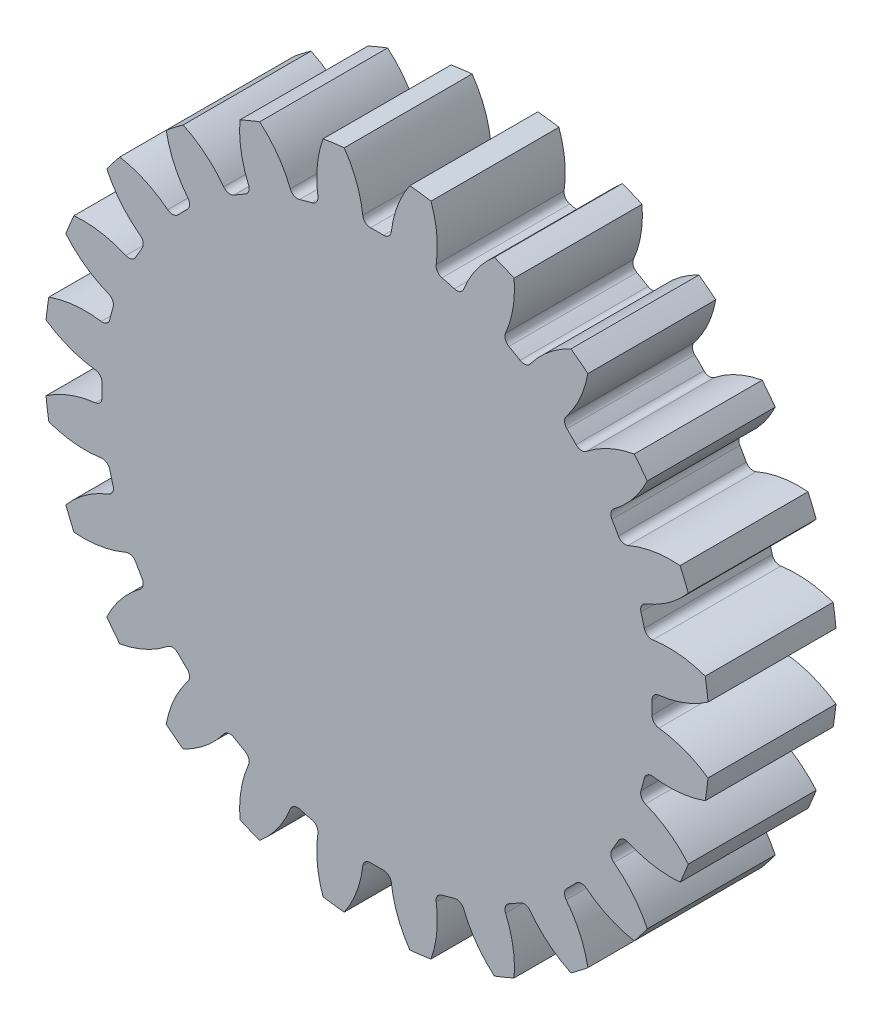
SolidWorks part; units mm, degrees
ref_plane "Front" through (0, 0, 0) normal (0, 0, 1) x (1, 0, 0)
ref_plane "Top" through (0, 0, 0) normal (0, 1, 0) x (1, 0, 0)
ref_plane "Right" through (0, 0, 0) normal (1, 0, 0) x (0, 0, -1)
sketch "Sketch2" plane through (0, 0, 0) normal (0, 0, 1) x (1, 0, 0)
  circle A0 centre (0, 0) radius 21.5
  circle A1 centre (0, 0) radius 24
  circle A2 centre (0, 0) radius 26
  dimension "D1" = 48
  dimension "D2" = 52
  dimension "D3" = 4.5
extrude "Boss-Extrude1" add sketch "Sketch2" along normal mid plane 10 contours A2
sketch "Sketch3" plane through (0, 0, 0) normal (0, 0, 1) x (1, 0, 0)
  line L0 (0, 0) -> (0, 26) construction
  line L1 (-1.5697, 23.9486) -> (1.5697, 23.9486) construction
  line L2 (0, 0) -> (-1.0694, 21.4734) construction
  line L3 (0, 19.636) -> (-2.6334, 26.8713) construction
  line L4 (0, 0) -> (3.3937, 25.7776) construction
  line L5 (1.5697, 23.9486) -> (4.6822, 23.5388) construction
  circle A0 centre (0, 0) radius 26 construction
  arc A1 (-1.0694, 21.4734) -> (-3.3054, 26.7969) centre (-9.5277, 21.0521) ccw
  arc A2 (1.0694, 21.4734) -> (3.3054, 26.7969) centre (9.5277, 21.0521) cw
  circle A3 centre (0, 0) radius 21.5 construction
  arc A4 (1.0694, 21.4734) -> (-1.0694, 21.4734) centre (0, 0) ccw
  circle A6 centre (0, 0) radius 24 construction
  circle A7 centre (0, 0) radius 27
  arc A8 (3.3054, 26.7969) -> (-3.3054, 26.7969) centre (0, 0) ccw
  circle A9 centre (0, 0) radius 26 construction
  dimension "D2" = 20
  dimension "D3" = 7.5
  dimension "D1" = 1
extrude "Cut-Extrude1" cut sketch "Sketch3" against normal through all both and the other way through all contours A8 A1 A4 A2
fillet "Fillet1" radius 0.6 2 edges at (1.0694, 21.4734, 0) (-1.0694, 21.4734, 0)
pattern_circular "CirPattern1" count 24 over 360 about axis through (0, 0, 0) along (0, 0, 1) of "Fillet1", "Cut-Extrude1"
equation "\"teeth\"= 24"
equation "\"module\"= 2mm"
equation "\"D1@Sketch2\"=\"module\"*\"teeth\""
equation "\"D2@Sketch2\"=(\"teeth\"+2)*\"module\""
equation "\"pressure_angle\"= 20deg"
equation "\"D2@Sketch3\"=\"pressure_angle\""
equation "\"D3@Sketch3\"=180/\"teeth\""
equation "\"D1@Fillet1\"=0.3 * \"module\""
equation "\"D1@CirPattern1\"=\"teeth\""
equation "\"D3@Sketch2\"=\"module\" * if ( \"module\" >= 1.25 , 2.25 , 2.4 )"
